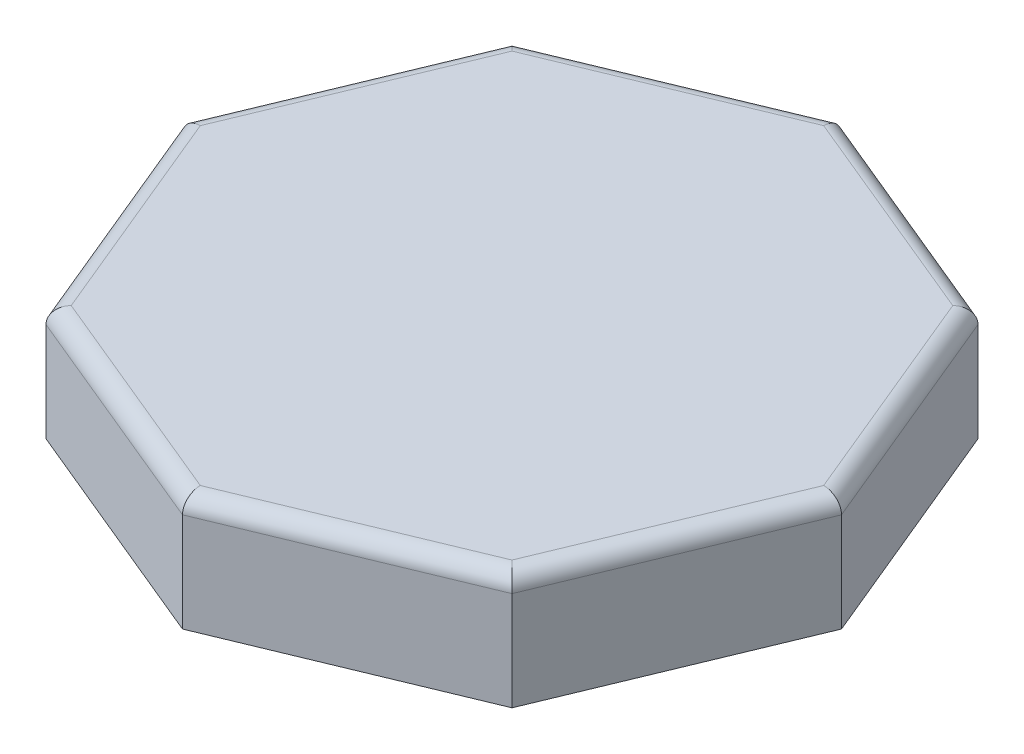
SolidWorks part; units mm, degrees
ref_plane "Front Plane" through (0, 0, 0) normal (0, 0, 1) x (1, 0, 0)
ref_plane "Top Plane" through (0, 0, 0) normal (0, 1, 0) x (1, 0, 0)
ref_plane "Right Plane" through (0, 0, 0) normal (1, 0, 0) x (0, 0, -1)
sketch "Sketch3" plane through (0, 0, 0) normal (0, 1, 0) x (1, 0, 0)
  line L0 (0, 0) -> (0, -199.9041) construction
  line L3 (0, 0) -> (0, 199.9041) construction
  line L4 (0, 0) -> (199.9041, 0) construction
  line L5 (0, 0) -> (-199.9041, 0) construction
  line L6 (0, 0) -> (141.3536, -141.3536) construction
  line L7 (0, 0) -> (141.3536, 141.3536) construction
  line L8 (0, 0) -> (-141.3536, 141.3536) construction
  line L9 (0, 0) -> (-141.3536, -141.3536) construction
  line L10 (0, 199.9041) -> (-141.3536, 141.3536)
  line L11 (-141.3536, 141.3536) -> (-199.9041, 0)
  line L12 (-199.9041, 0) -> (-141.3536, -141.3536)
  line L13 (-141.3536, -141.3536) -> (0, -199.9041)
  line L14 (0, -199.9041) -> (141.3536, -141.3536)
  line L15 (141.3536, -141.3536) -> (199.9041, 0)
  line L16 (199.9041, 0) -> (141.3536, 141.3536)
  line L17 (141.3536, 141.3536) -> (0, 199.9041)
  circle A0 centre (0, 0) radius 199.9041 construction
  dimension "D1" = 153
extrude "Boss-Extrude1" add sketch "Sketch3" along normal blind 70
shell "Shell1" thickness 3
ref_plane "Plane1" through (0, 90, 0) normal (0, 1, 0) x (1, 0, 0)
sketch "Sketch4" plane through (0, 90, 0) normal (0, 1, 0) x (1, 0, 0)
  point P0 (0, 0)
fillet "Fillet1" radius 10 8 edges at (170.6289, 70, 70.6768) (70.6768, 70, 170.6289) (-70.6768, 70, 170.6289) (-170.6289, 70, 70.6768) (-170.6289, 70, -70.6768) (-70.6768, 70, -170.6289) (70.6768, 70, -170.6289) (170.6289, 70, -70.6768)
fillet "Fillet2" radius 3 8 edges at (167.8572, 67, -69.5287) (167.8572, 67, 69.5287) (69.5287, 67, 167.8572) (-69.5287, 67, 167.8572) (-167.8572, 67, 69.5287) (-167.8572, 67, -69.5287) (-69.5287, 67, -167.8572) (69.5287, 67, -167.8572)
